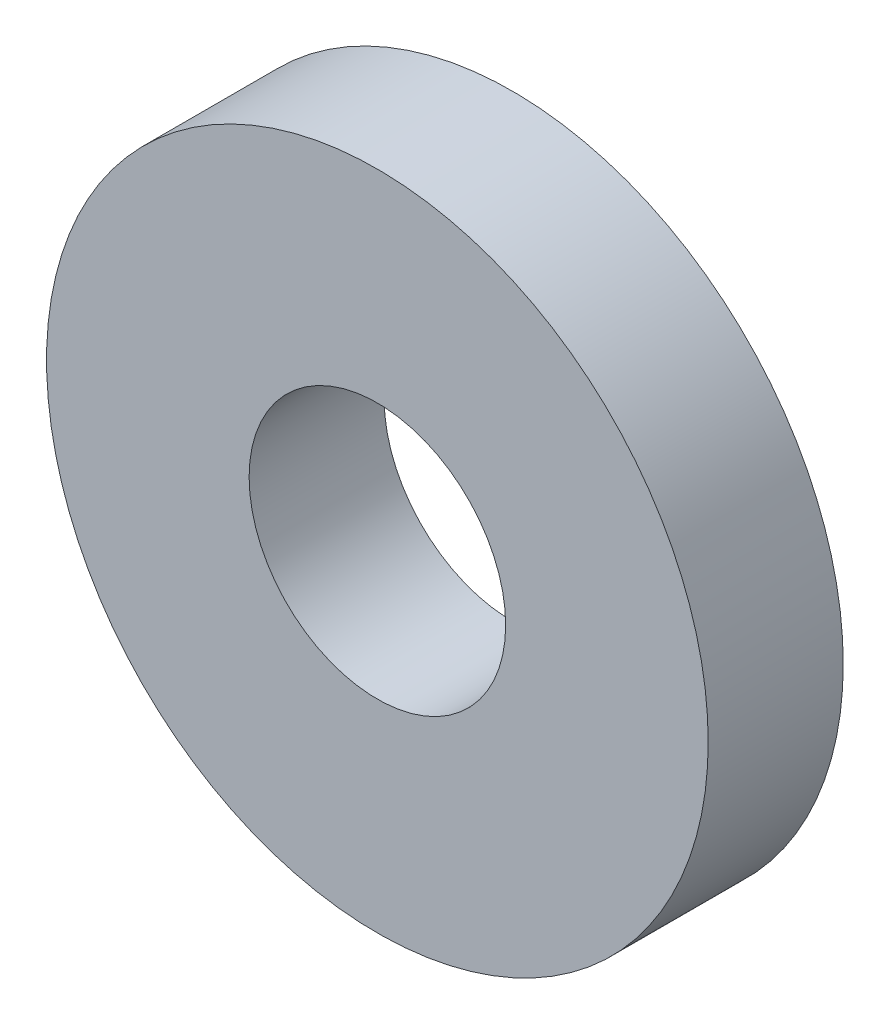
SolidWorks part; units mm, degrees
ref_plane "Front Plane" through (0, 0, 0) normal (0, 0, 1) x (1, 0, 0)
ref_plane "Top Plane" through (0, 0, 0) normal (0, 1, 0) x (1, 0, 0)
ref_plane "Right Plane" through (0, 0, 0) normal (1, 0, 0) x (0, 0, -1)
sketch "Sketch1" plane through (0, 0, 0) normal (0, 0, 1) x (1, 0, 0)
  circle A0 centre (0, 0) radius 0.95
  circle A1 centre (0, 0) radius 2.45
  dimension "D1" = 1.9
  dimension "D2" = 4.9
extrude "Boss-Extrude1" add sketch "Sketch1" along normal blind 1
